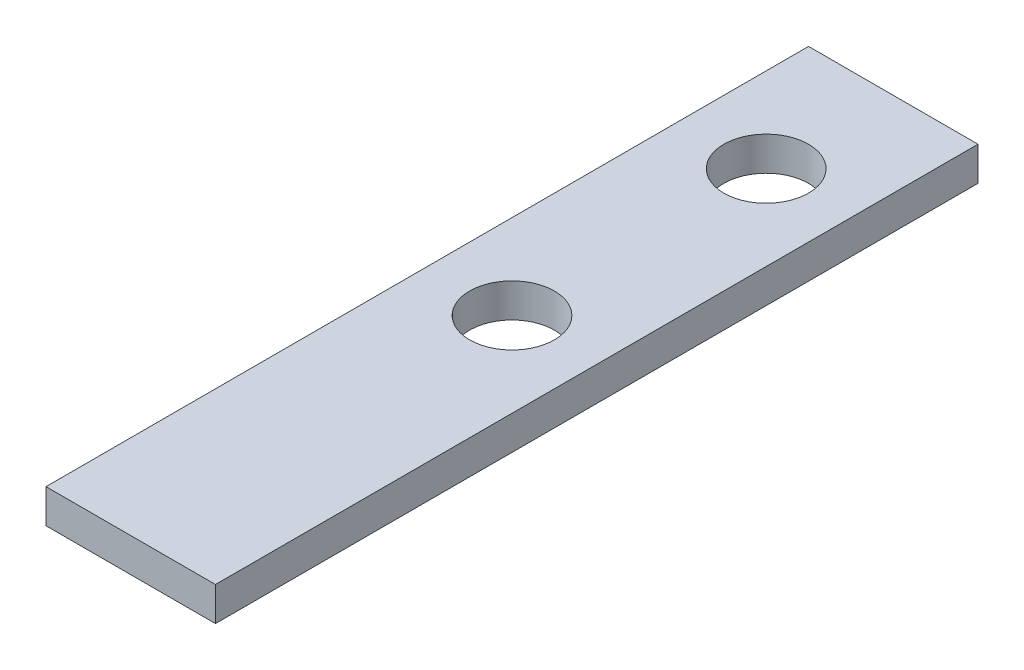
SolidWorks part; units mm, degrees
ref_plane "Спереди" through (0, 0, 0) normal (0, 0, 1) x (1, 0, 0)
ref_plane "Сверху" through (0, 0, 0) normal (0, 1, 0) x (1, 0, 0)
ref_plane "Справа" through (0, 0, 0) normal (1, 0, 0) x (0, 0, -1)
sketch "Эскиз1" plane through (0, 0, 0) normal (0, 1, 0) x (1, 0, 0)
  line L1 (0, 0) -> (20, 0)
  line L2 (0, 0) -> (0, 90)
  line L3 (0, 90) -> (20, 90)
  line L4 (20, 0) -> (20, 90)
  circle A0 centre (10, 45) radius 5
  circle A1 centre (10, 75) radius 5
  dimension "D1" = 2
extrude "Бобышка-Вытянуть1" add sketch "Эскиз1" along normal blind 4
